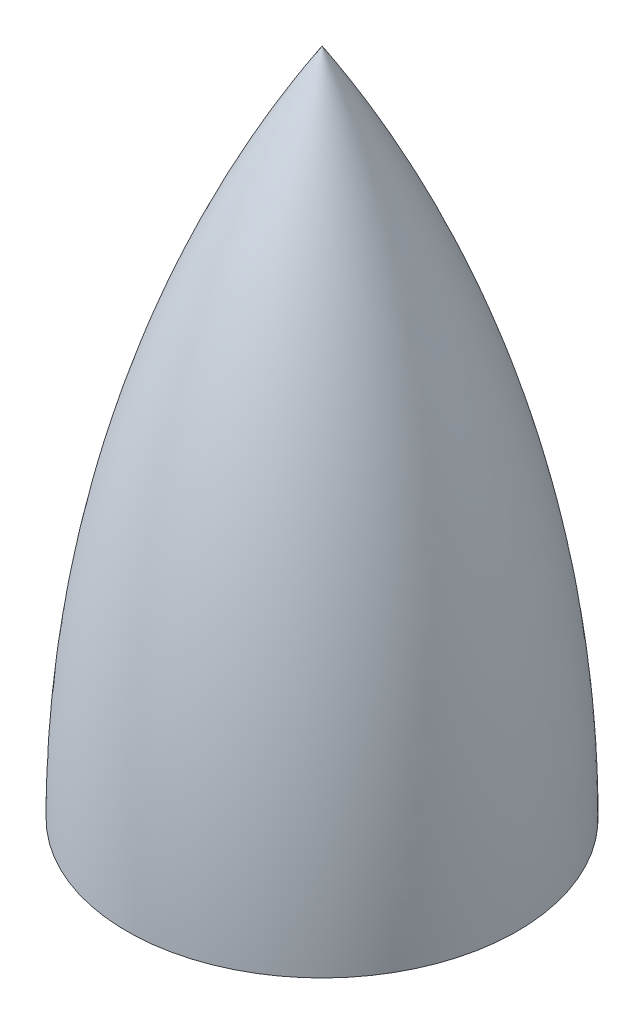
SolidWorks part; units mm, degrees
ref_plane "Front Plane" through (0, 0, 0) normal (0, 0, 1) x (1, 0, 0)
ref_plane "Top Plane" through (0, 0, 0) normal (0, 1, 0) x (1, 0, 0)
ref_plane "Right Plane" through (0, 0, 0) normal (1, 0, 0) x (0, 0, -1)
sketch "Sketch1" plane through (0, 0, 0) normal (0, 0, 1) x (1, 0, 0)
  line L2 (0, 0) -> (3500, 0)
  line L3 (0, 0) -> (0, 12000)
  arc A2 (3500, 0) -> (0, 12000) centre (-18821, 0.125) ccw
  dimension "D1" = 3500
  dimension "D3" = 12000
revolve "Revolve1" add sketch "Sketch1" angle 360 about L3
